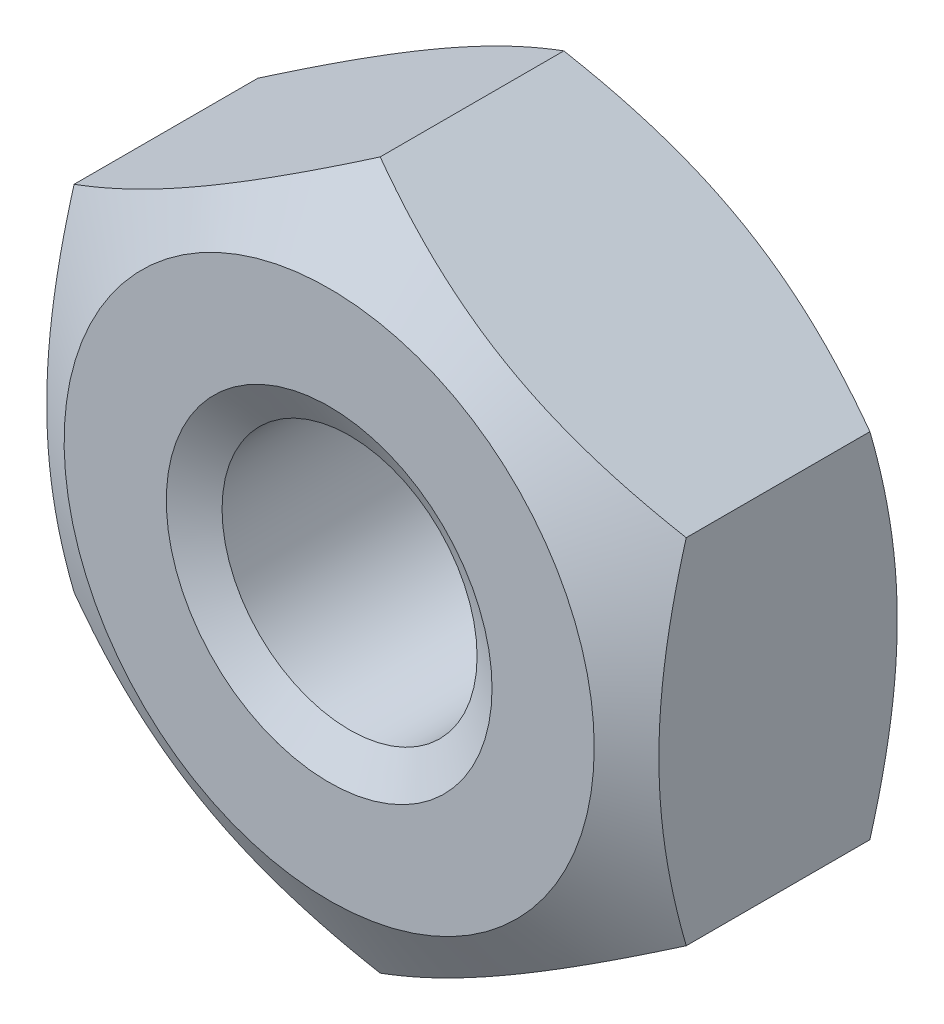
SolidWorks part; units mm, degrees
ref_plane "Front Plane" through (0, 0, 0) normal (0, 0, 1) x (1, 0, 0)
ref_plane "Top Plane" through (0, 0, 0) normal (0, 1, 0) x (1, 0, 0)
ref_plane "Right Plane" through (0, 0, 0) normal (1, 0, 0) x (0, 0, -1)
sketch "Sketch1" plane through (0, 0, 0) normal (0, 0, 1) x (1, 0, 0)
  line L1 (0, 1.7321) -> (-1.5, 0.866)
  line L2 (-1.5, 0.866) -> (-1.5, -0.866)
  line L3 (-1.5, -0.866) -> (0, -1.7321)
  line L4 (0, -1.7321) -> (1.5, -0.866)
  line L5 (1.5, -0.866) -> (1.5, 0.866)
  line L6 (1.5, 0.866) -> (0, 1.7321)
  circle A0 centre (0, 0) radius 1.5 construction
  dimension "D1" = 3
extrude "Boss-Extrude1" add sketch "Sketch1" against normal blind 1.4
sketch "Sketch2" plane through (0, 0, 0) normal (1, 0, 0) x (0, 0, -1)
  line L0 (0, -1.299) -> (0.25, -1.7321)
  line L1 (0, -1.7321) -> (0, -0.866) construction
  line L2 (1.4, -1.7321) -> (0, -1.7321) construction
  line L3 (0.25, -1.7321) -> (0, -1.7321)
  line L4 (0, -1.7321) -> (0, -1.299)
  line L5 (0, 0) -> (1.4, 0) construction
  line L6 (0, -0.866) -> (0, 0.866) construction
  line L7 (1.4, -0.866) -> (1.4, 0.866) construction
  line L8 (0.7, 0) -> (0.7, 1.7321) construction
  line L9 (1.4, 1.7321) -> (0, 1.7321) construction
  line L10 (1.4, -1.7321) -> (1.4, -1.299)
  line L11 (1.15, -1.7321) -> (1.4, -1.7321)
  line L12 (1.4, -1.299) -> (1.15, -1.7321)
  dimension "D1" = 30
revolve "Cut-Revolve1" cut sketch "Sketch2" angle 360 about L5
hole_wizard "M1.7 Tapped Hole1" positions "Sketch4" profile "Sketch3" tap size "M1.6" standard "DIN" end condition through all
sketch "Sketch4" plane through (0, 0, 0) normal (0, 0, 1) x (1, 0, 0)
  point P0 (0, 0)
sketch "Sketch3" plane through (0, 0, 0) normal (1, 0, 0) x (0, -1, 0)
  line L0 (0, 0) -> (0, 1.4)
  line L1 (0, 1.4) -> (0.625, 1.4)
  line L2 (0.625, 1.4) -> (0.625, 0)
  line L5 (0.625, 0) -> (0, 0)
  line L11 (0, -6.35) -> (0, 107.95) construction
  dimension "Thru Tap Drill Dia." = 1.25
  dimension "Thru Tap Drill Depth" = 1.4
cosmetic thread "Hole Thread1" parameters "D2"=1.6
sketch "Sketch5" plane through (0, 0, 0) normal (1, 0, 0) x (0, 0, -1)
  line L2 (0, 0) -> (1.4, 0) construction
  line L3 (1.4, -1.299) -> (1.4, 1.299) construction
chamfer "Chamfer1" distance 0.1 angle 60 1 edges at (0.625, 0, 0)
